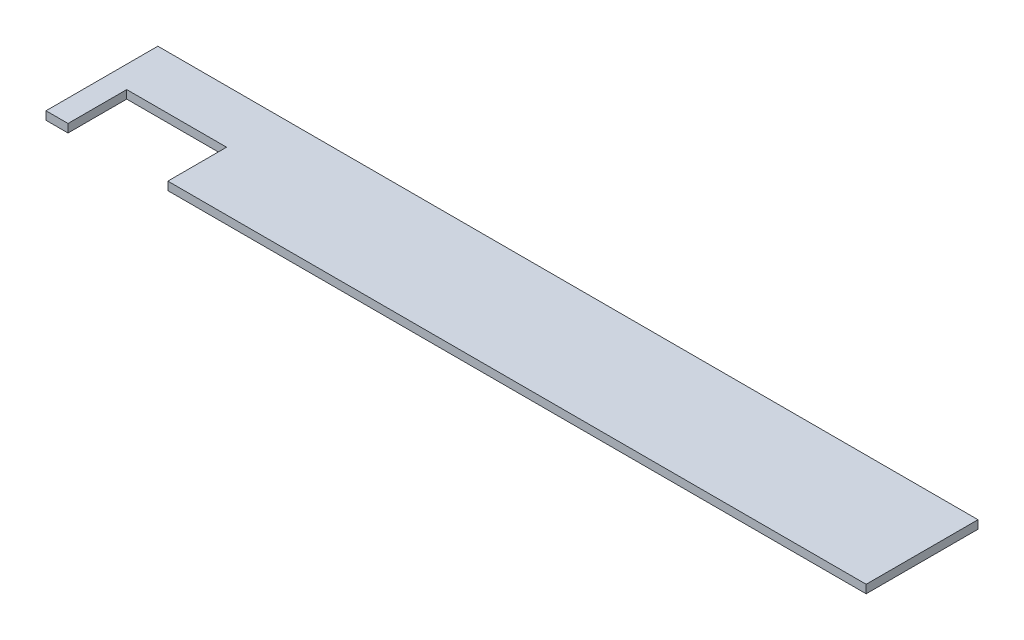
SolidWorks part; units mm, degrees
material "Acrylic (Medium-high impact)"
ref_plane "Front Plane" through (0, 0, 0) normal (0, 0, 1) x (1, 0, 0)
ref_plane "Top Plane" through (0, 0, 0) normal (0, 1, 0) x (1, 0, 0)
ref_plane "Right Plane" through (0, 0, 0) normal (1, 0, 0) x (0, 0, -1)
sketch "Sketch1" plane through (0, 0, 0) normal (0, 1, 0) x (1, 0, 0)
  line L0 (-185, -73.025) -> (373.7224, -73.025)
  line L1 (175, 3.175) -> (-175, 3.175)
  line L2 (-185, -6.825) -> (-185, 3.175)
  line L3 (357.3724, -3.175) -> (-168.65, -3.175) construction
  line L4 (-185, 3.175) -> (-175, 3.175)
  line L5 (175, 3.175) -> (373.7224, 3.175)
  line L6 (373.7224, 3.175) -> (373.7224, -6.825)
  line L8 (-185, -6.825) -> (-185, -73.025)
  line L9 (-185, -73.025) -> (-178.65, -73.025) construction
  line L10 (-178.65, -13.175) -> (-178.65, -73.025) construction
  line L12 (373.7224, -6.825) -> (373.7224, -73.025)
  line L13 (373.7224, -73.025) -> (367.3724, -73.025) construction
  line L14 (367.3724, -13.175) -> (367.3724, -73.025) construction
  arc A0 (357.3724, -3.175) -> (367.3724, -13.175) centre (357.3724, -13.175) cw construction
  arc A1 (-168.65, -3.175) -> (-178.65, -13.175) centre (-168.65, -13.175) ccw construction
  point P0 (0, 0)
  point P17 (373.7224, 3.175)
  point P20 (-185, 3.175)
  dimension "D10" = 10
  dimension "D2" = 558.7224
  dimension "D3" = 76.2
  dimension "D4" = 76.2
  dimension "D5" = 185
  dimension "D6" = 3.175
  dimension "D7" = 3.175
  dimension "D8" = 6.35
  dimension "D9" = 6.35
extrude "Boss-Extrude1" add sketch "Sketch1" along normal blind 5.6388
sketch "Sketch2" plane through (0, 5.6388, 0) normal (0, 1, 0) x (1, 0, 0)
  line L1 (-185, -73.025) -> (373.7224, -73.025) construction
  line L2 (-170, -73.025) -> (-102, -73.025)
  line L3 (-170, -73.025) -> (-170, -33.025)
  line L4 (-170, -33.025) -> (-102, -33.025)
  line L6 (-102, -73.025) -> (-102, -33.025)
  line L7 (-185, 3.175) -> (-185, -73.025) construction
  point P8 (-174.0031, -61.6673)
  dimension "D1" = 40
  dimension "D2" = 15
  dimension "D3" = 68
extrude "Cut-Extrude1" cut sketch "Sketch2" against normal through all
